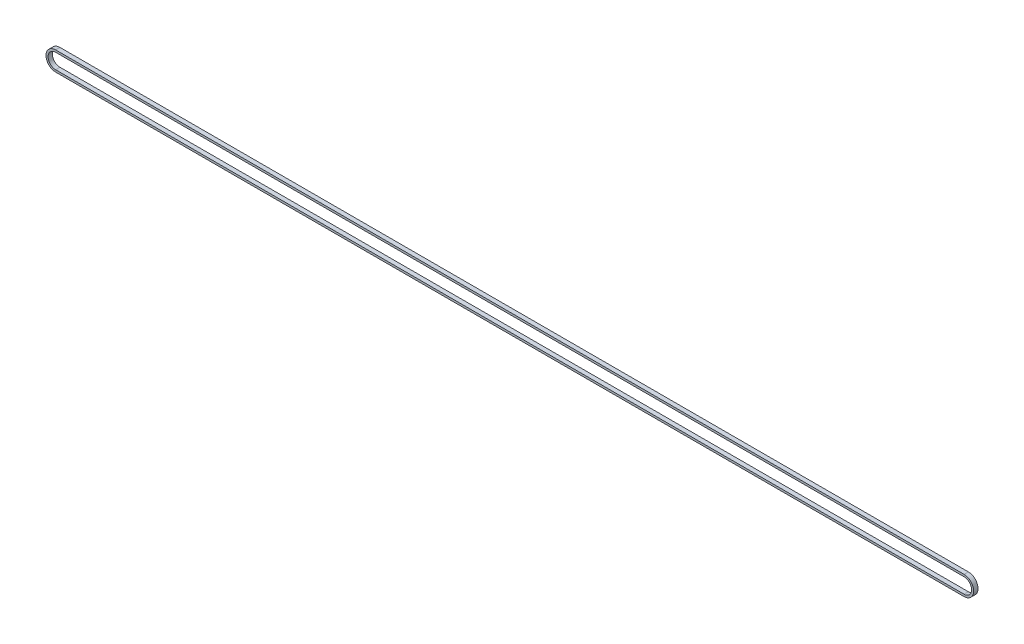
SolidWorks part; units mm, degrees
material "Rubber"
ref_plane "Front Plane" through (0, 0, 0) normal (0, 0, 1) x (1, 0, 0)
ref_plane "Top Plane" through (0, 0, 0) normal (0, 1, 0) x (1, 0, 0)
ref_plane "Right Plane" through (0, 0, 0) normal (1, 0, 0) x (0, 0, -1)
sketch "Sketch1" plane through (0, 0, 0) normal (0, 0, 1) x (1, 0, 0)
  line L0 (0, 0) -> (1051.8, 0) construction
  line L1 (0, 8.75) -> (1051.8, 8.75)
  line L2 (1051.8, -8.75) -> (0, -8.75)
  arc A0 (0, 8.75) -> (0, -8.75) centre (0, 0) ccw
  arc A1 (1051.8, -8.75) -> (1051.8, 8.75) centre (1051.8, 0) ccw
  dimension "D1" = 17.5
  dimension "D2" = 1051.8
extrude "Extrude-Thin1" add sketch "Sketch1" along normal mid plane 5 thin thin type one direction wall 2.4
